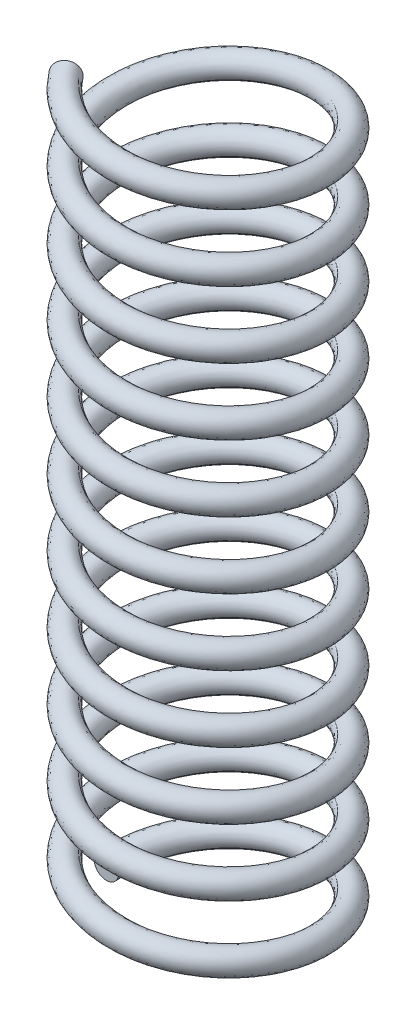
SolidWorks part; units mm, degrees
material "Plain Carbon Steel"
ref_plane "Front Plane" through (0, 0, 0) normal (0, 0, 1) x (1, 0, 0)
ref_plane "Top Plane" through (0, 0, 0) normal (0, 1, 0) x (1, 0, 0)
ref_plane "Right Plane" through (0, 0, 0) normal (1, 0, 0) x (0, 0, -1)
sketch "Sketch1" plane through (0, 0, 0) normal (0, 1, 0) x (1, 0, 0)
  circle A0 centre (0, 0) radius 12.3825
  dimension "D1" = 24.765
curve "Helix/Spiral1" pitch 7.2355 height 78.867 turns 10.9
sketch "Sketch2" plane through (0, 0, 0) normal (0, 0, 1) x (1, 0, 0)
  circle A0 centre (-11.049, 1.3335) radius 1.3335
  point P2 (0, 0)
  point P4 (-10.1611, 1.8649)
  dimension "D1" = 2.667
  dimension "D2" = 1.3335
  dimension "D3" = 11.049
sweep "Sweep1" add profiles "Sketch2" path "Helix/Spiral1"
equation "\"D2@Sketch2\"=\"D1@Sketch2\"/2"
equation "\"D3@Sketch2\"=(.975-\"D1@Sketch2\")/2"
